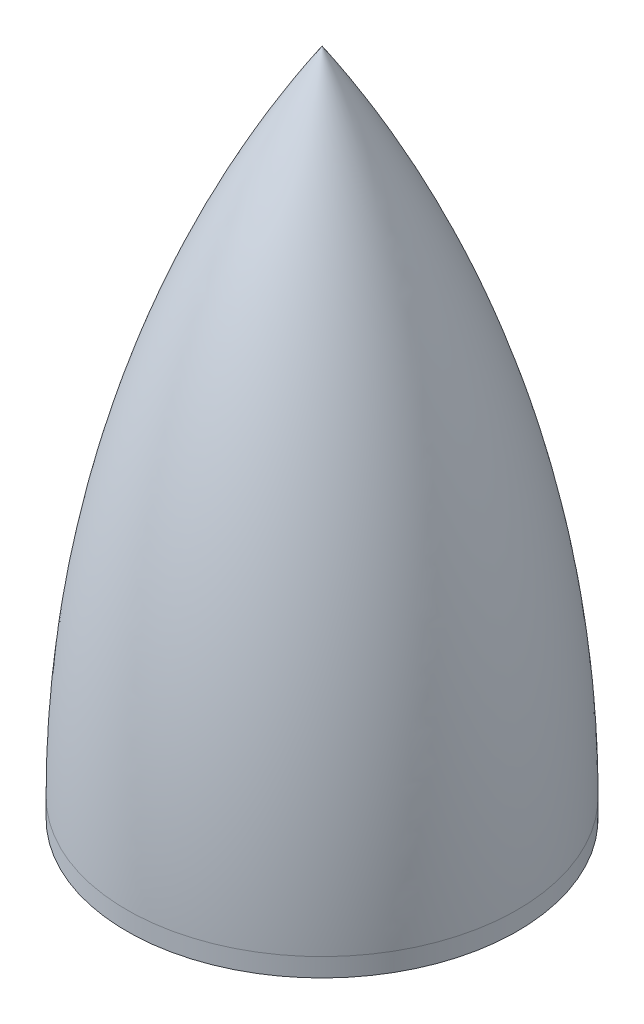
SolidWorks part; units mm, degrees
ref_plane "Front Plane" through (0, 0, 0) normal (0, 0, 1) x (1, 0, 0)
ref_plane "Top Plane" through (0, 0, 0) normal (0, 1, 0) x (1, 0, 0)
ref_plane "Right Plane" through (0, 0, 0) normal (1, 0, 0) x (0, 0, -1)
sketch "Sketch1" plane through (0, 0, 0) normal (0, 0, 1) x (1, 0, 0)
  line L0 (0, 0) -> (0, 65.3751) construction
  line L1 (-1.5875, 0) -> (-22.225, 0)
  line L2 (-22.225, 0) -> (-22.225, 2.1082)
  line L3 (-1.5875, 2.1082) -> (-1.5875, 6.35)
  line L4 (-1.5875, 0) -> (-1.5875, 2.1082)
  line L5 (-6.35, 2.1082) -> (-21.1836, 2.1082)
  line L6 (0, 76.2) -> (0, 73.8451)
  line L10 (-1.5875, 6.35) -> (-6.35, 6.35)
  line L11 (-6.35, 6.35) -> (-6.35, 2.1082)
  arc A0 (-22.225, 2.1082) -> (0, 76.2) centre (112.3879, 2.1082) cw
  arc A1 (-21.1836, 2.1082) -> (0, 73.8451) centre (113.4272, 1.3544) cw
  dimension "D1" = 1.0414
  dimension "D2" = 3.175
  dimension "D3" = 76.2
  dimension "D4" = 2.1082
  dimension "D5" = 6.35
  dimension "D6" = 44.45
  dimension "D7" = 12.7
revolve "Revolve1" add sketch "Sketch1" angle 360 about L0
